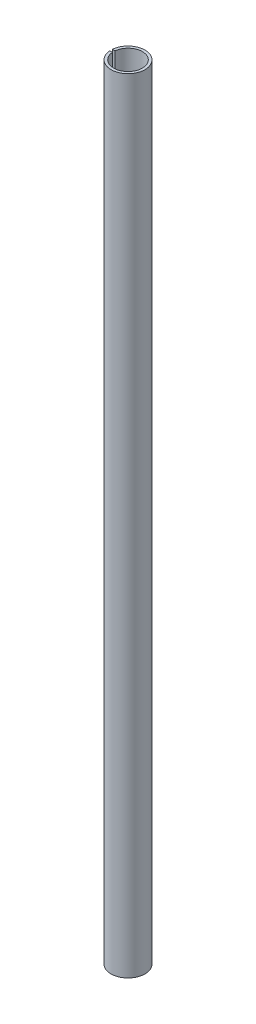
SolidWorks part; units mm, degrees
material "普通碳钢"
ref_plane "前视基准面" through (0, 0, 0) normal (0, 0, 1) x (1, 0, 0)
ref_plane "上视基准面" through (0, 0, 0) normal (0, 1, 0) x (1, 0, 0)
ref_plane "右视基准面" through (0, 0, 0) normal (1, 0, 0) x (0, 0, -1)
sketch "草图1" plane through (0, 0, 0) normal (0, 1, 0) x (1, 0, 0)
  circle A0 centre (0, 0) radius 11
  circle A1 centre (0, 0) radius 13
  dimension "D1" = 22
  dimension "D2" = 26
extrude "凸台-拉伸1" add sketch "草图1" along normal blind 600
sketch "草图2" plane through (0, 0, 0) normal (1, 0, 0) x (0, 0, -1)
  line L0 (0, 0) -> (0, 43.4676) construction
  line L1 (0, 600) -> (0, 534.0047) construction
  line L2 (13, 600) -> (-13, 600) construction
  line L3 (-13, 0) -> (13, 0) construction
  line L4 (-1, 600) -> (1, 600)
  line L5 (-1, 600) -> (-1, 570)
  line L6 (-1, 570) -> (1, 570)
  line L7 (1, 600) -> (1, 570)
  line L8 (-1, 30) -> (1, 30)
  line L9 (-1, 30) -> (-1, 0)
  line L10 (-1, 0) -> (1, 0)
  line L11 (1, 30) -> (1, 0)
  dimension "D1" = 2
  dimension "D2" = 30
  dimension "D3" = 2
  dimension "D4" = 30
extrude "切除-拉伸1" cut sketch "草图2" against normal through all
